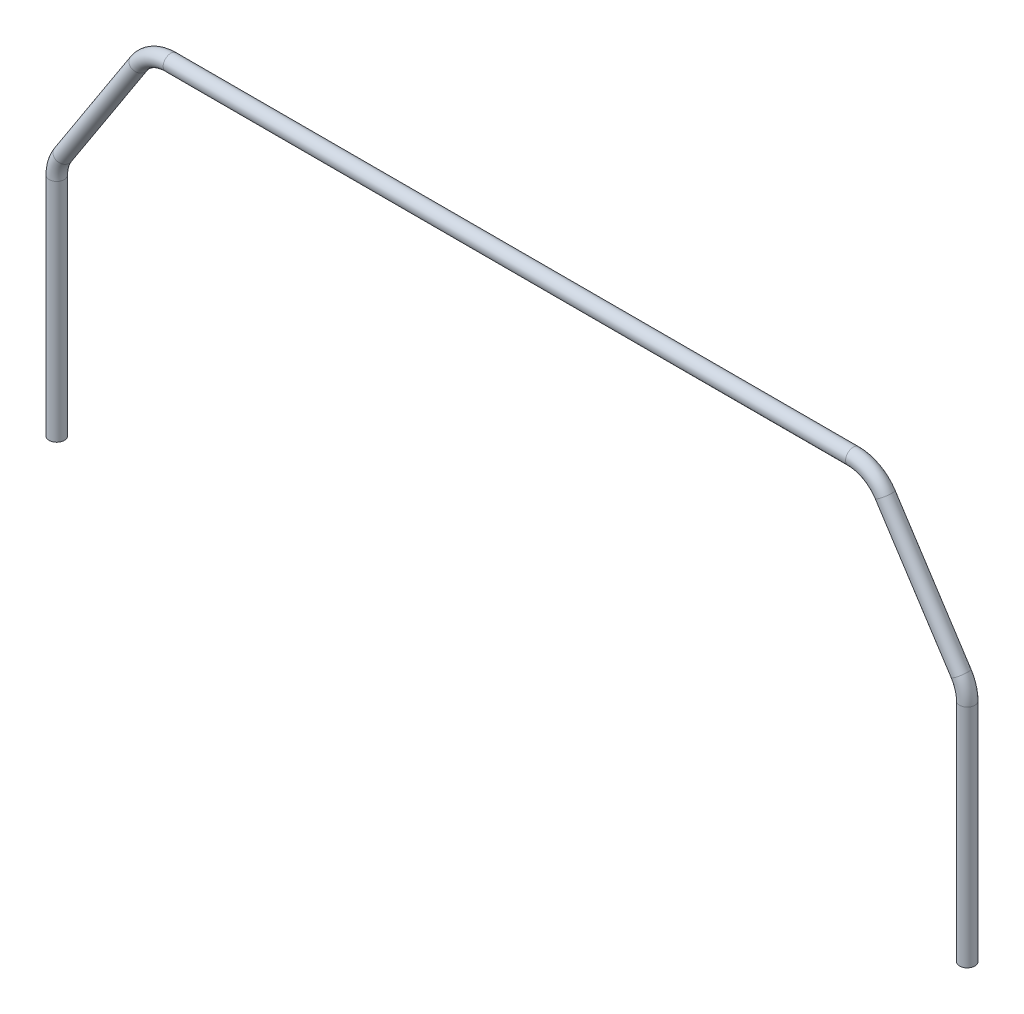
SolidWorks part; units mm, degrees
ref_plane "Front Plane" through (0, 0, 0) normal (0, 0, 1) x (1, 0, 0)
ref_plane "Top Plane" through (0, 0, 0) normal (0, 1, 0) x (1, 0, 0)
ref_plane "Right Plane" through (0, 0, 0) normal (1, 0, 0) x (0, 0, -1)
sketch "Sketch6" plane through (0, 0, 0) normal (0, 0, 1) x (1, 0, 0)
  line L0 (-48.5706, 0) -> (46.9509, 0) construction
  line L1 (0, -34.6277) -> (0, 60.199) construction
  line L2 (-119.5, 49.2933) -> (-119.5, -10)
  line L3 (-117.888, 54.7377) -> (-97.9569, 85.4444)
  line L4 (-89.5689, 90) -> (89.5689, 90)
  line L5 (117.888, 54.7377) -> (97.9569, 85.4444)
  line L6 (119.5, 49.2933) -> (119.5, -10)
  arc A0 (-97.9569, 85.4444) -> (-89.5689, 90) centre (-89.5689, 80) cw
  arc A1 (-119.5, 49.2933) -> (-117.888, 54.7377) centre (-109.5, 49.2933) cw
  arc A2 (97.9569, 85.4444) -> (89.5689, 90) centre (89.5689, 80) ccw
  arc A3 (119.5, 49.2933) -> (117.888, 54.7377) centre (109.5, 49.2933) ccw
  point P7 (0, 60.199)
  point P10 (0, 42.7071)
  point P13 (-95, 90)
  point P16 (-119.5, 52.2541)
  point P18 (0, 90)
  dimension "D6" = 10
  dimension "D1" = 10
  dimension "D2" = 119.5
  dimension "D3" = 45
  dimension "D4" = 95
  dimension "D5" = 90
sweep "Sweep2" add path "Sketch6" circular profile diameter 4 parameters "D3"=4
